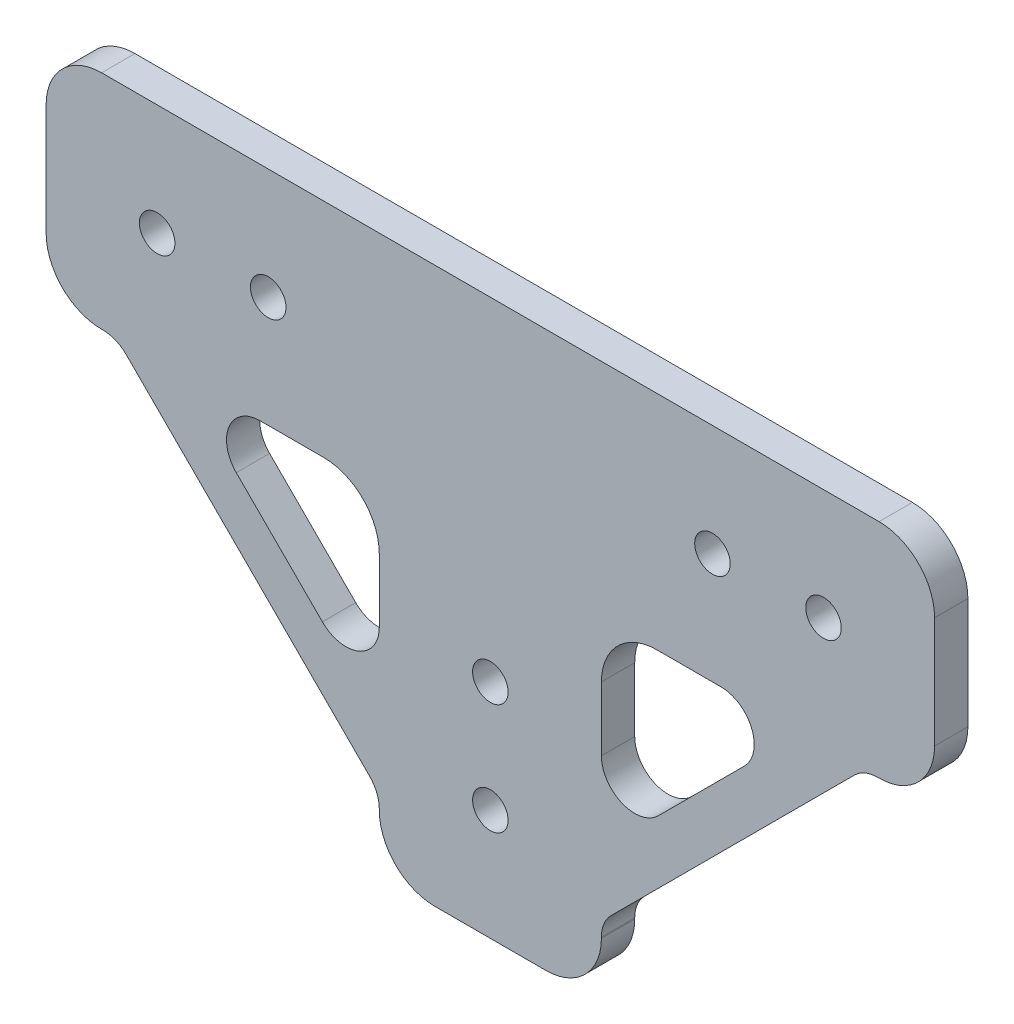
SolidWorks part; units mm, degrees
material "A-玻璃纤维"
ref_plane "前视基准面" through (0, 0, 0) normal (0, 0, 1) x (1, 0, 0)
ref_plane "上视基准面" through (0, 0, 0) normal (0, 1, 0) x (1, 0, 0)
ref_plane "右视基准面" through (0, 0, 0) normal (1, 0, 0) x (0, 0, -1)
sketch "草图1" plane through (0, 0, 0) normal (0, 0, 1) x (1, 0, 0)
  line L0 (0, 119.3087) -> (0, -110.3884) construction
  line L1 (212.4937, 0) -> (-225.8741, 0) construction
  line L2 (-40, 0) -> (-40, 20)
  line L3 (-40, 20) -> (40, 20)
  line L4 (40, 20) -> (40, 0)
  line L5 (40, 0) -> (10, 0)
  line L6 (10, 0) -> (10, -30)
  line L7 (10, -30) -> (-10, -30)
  line L8 (-10, -30) -> (-10, 0)
  line L9 (-10, 0) -> (-40, 0)
  circle A0 centre (-30, 10) radius 1.6
  circle A1 centre (-20, 10) radius 1.6
  circle A2 centre (0, -10) radius 1.6
  circle A3 centre (0, -20) radius 1.6
  circle A4 centre (20, 10) radius 1.6
  circle A5 centre (30, 10) radius 1.6
  dimension "D3" = 10
  dimension "D4" = 3.2
  dimension "D5" = 10
  dimension "D6" = 40
  dimension "D7" = 10
  dimension "D8" = 10
  dimension "D10" = 10
  dimension "D1" = 20
  dimension "D2" = 20
  dimension "D9" = 10
extrude "凸台-拉伸1" add sketch "草图1" along normal blind 3
fillet "圆角1" radius 5 8 edges at (-10, -30, 1.5) (10, -30, 1.5) (10, 0, 1.5) (-10, 0, 1.5) (40, 20, 1.5) (40, 0, 1.5) (-40, 0, 1.5) (-40, 20, 1.5)
sketch "草图2" plane through (0, 0, 0) normal (0, 0, -1) x (-1, 0, 0)
  line L0 (-33.6569, 0) -> (-10, -23.6569)
  line L1 (-15, 0) -> (-35, 0) construction
  line L2 (-10, -25) -> (-10, -5) construction
  line L3 (-10, -23.6569) -> (-10, -18)
  line L4 (-10, -18) -> (-28, 0)
  line L5 (-28, 0) -> (-33.6569, 0)
  line L6 (45.9845, 0) -> (-78.8076, 0) construction
  line L7 (0, 40.6393) -> (0, -62.1867) construction
  line L8 (10, -18) -> (28, 0)
  line L9 (10, -23.6569) -> (10, -18)
  line L10 (33.6569, 0) -> (10, -23.6569)
  line L11 (28, 0) -> (33.6569, 0)
  dimension "D1" = 4
  dimension "D2" = 18
  dimension "D3" = 45
extrude "凸台-拉伸2" add sketch "草图2" against normal blind 3
fillet "圆角2" radius 3 8 edges at (-10, -23.6569, 1.5) (-33.6569, 0, 1.5) (-28, 0, 1.5) (-10, -18, 1.5) (10, -18, 1.5) (10, -23.6569, 1.5) (33.6569, 0, 1.5) (28, 0, 1.5)
